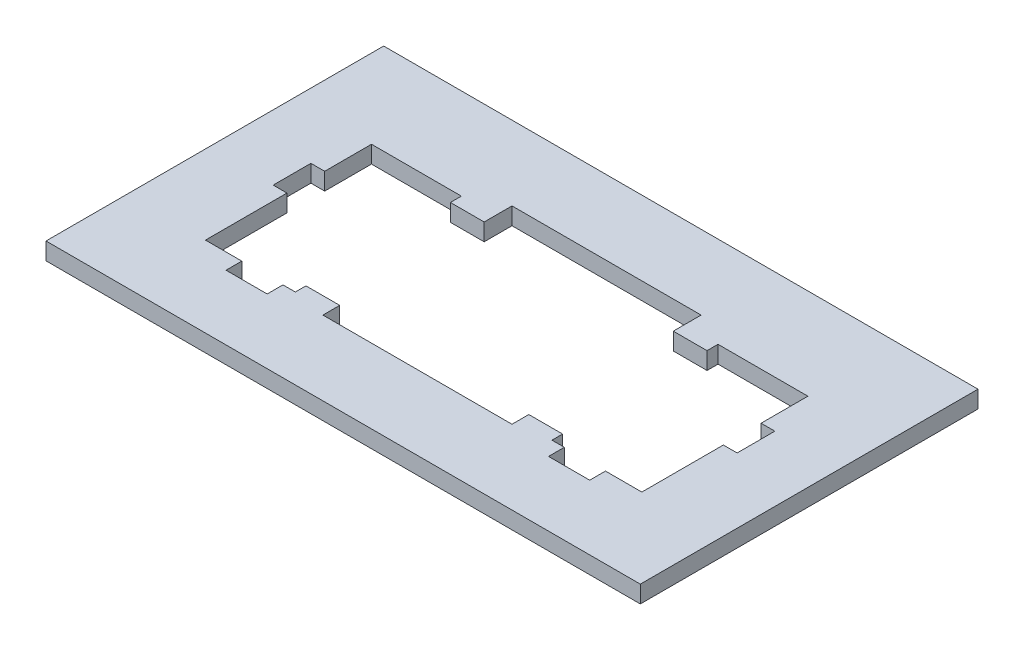
SolidWorks part; units mm, degrees
ref_plane "Front" through (0, 0, 0) normal (0, 0, 1) x (1, 0, 0)
ref_plane "Top" through (0, 0, 0) normal (0, 1, 0) x (1, 0, 0)
ref_plane "Right" through (0, 0, 0) normal (1, 0, 0) x (0, 0, -1)
sketch "Sketch1" plane through (0, 0, 0) normal (0, 1, 0) x (1, 0, 0)
  line L0 (-7, 4.9392) -> (-9.4996, 4.9392)
  line L1 (-22, 12.5) -> (22, 12.5)
  line L2 (-22, 12.5) -> (-22, -12.5)
  line L3 (-22, -12.5) -> (22, -12.5)
  line L4 (22, 12.5) -> (22, -12.5)
  line L5 (-22, 12.5) -> (22, -12.5) construction
  line L6 (-22, -12.5) -> (22, 12.5) construction
  line L7 (-7, 7) -> (7, 7)
  line L8 (-7, 7) -> (-7, -7)
  line L9 (-7, -7) -> (7, -7)
  line L10 (7, 7) -> (7, -7)
  line L11 (-7, 7) -> (7, -7) construction
  line L12 (-7, -7) -> (7, 7) construction
  line L13 (-9.4996, 4.9392) -> (-9.4996, 5.752)
  line L14 (-9.4996, 5.752) -> (-16.1544, 5.752)
  line L15 (-16.1544, 5.752) -> (-16.1544, 2.286)
  line L16 (-16.1544, 2.286) -> (-17.1742, 2.286)
  line L17 (-17.1742, 2.286) -> (-17.1742, -0.508)
  line L18 (-17.1742, -0.508) -> (-16.1544, -0.508)
  line L19 (-16.1544, -0.508) -> (-16.1544, -6.5416)
  line L20 (-16.1544, -6.5416) -> (-13.462, -6.5416)
  line L21 (-13.462, -6.5416) -> (-13.462, -7.71)
  line L22 (-13.462, -7.71) -> (-10.414, -7.71)
  line L23 (-10.414, -7.71) -> (-10.414, -6.5416)
  line L24 (-10.414, -6.5416) -> (-9.4996, -6.5416)
  line L25 (-9.4996, -6.5416) -> (-9.4996, -5.7542)
  line L26 (-9.4996, -5.7542) -> (-7, -5.7542)
  line L27 (0, 0) -> (-28.61, 0) construction
  line L28 (-11.938, -7.71) -> (-11.938, 13.6054) construction
  line L29 (0, 0) -> (0, 7) construction
  line L30 (9.4996, -5.7542) -> (7, -5.7542)
  line L31 (7, 4.9392) -> (9.4996, 4.9392)
  line L32 (9.4996, -6.5416) -> (9.4996, -5.7542)
  line L33 (10.414, -6.5416) -> (9.4996, -6.5416)
  line L34 (10.414, -7.71) -> (10.414, -6.5416)
  line L35 (13.462, -7.71) -> (10.414, -7.71)
  line L36 (13.462, -6.5416) -> (13.462, -7.71)
  line L37 (16.1544, -6.5416) -> (13.462, -6.5416)
  line L38 (16.1544, -0.508) -> (16.1544, -6.5416)
  line L39 (17.1742, -0.508) -> (16.1544, -0.508)
  line L40 (17.1742, 2.286) -> (17.1742, -0.508)
  line L41 (16.1544, 2.286) -> (17.1742, 2.286)
  line L42 (16.1544, 5.752) -> (16.1544, 2.286)
  line L43 (9.4996, 5.752) -> (16.1544, 5.752)
  line L44 (9.4996, 4.9392) -> (9.4996, 5.752)
  line L45 (11.938, -7.71) -> (11.938, 13.6054) construction
  point P0 (0, 0)
  point P6 (0, 0)
  point P50 (0, 0)
  point P51 (0, 0)
  dimension "D1" = 44
  dimension "D2" = 25
  dimension "D3" = 14
  dimension "D4" = 14
  dimension "D5" = 6.6548
  dimension "D6" = 0.8128
  dimension "D7" = 2.794
  dimension "D8" = 0.508
  dimension "D9" = 6.5416
  dimension "D10" = 3.048
  dimension "D11" = 12.2936
  dimension "D12" = 0.7874
  dimension "D13" = 13.462
  dimension "D14" = 23.876
  dimension "D15" = 4.2164
extrude "Boss-Extrude1" add sketch "Sketch1" along normal blind 1.524 contours L4 L1 L2 L3 L31 L44 L43 L42 L41 L40 L39 L38 L37 L36 L35 L34 L33 L32 L30 L10 L9 L8 L26 L25 L24 L23 L22 L21 L20 L19 L18 L17 L16 L15 L14 L13 L0 L7
chamfer "Chamfer1" distance 0.25 angle 45 40 edges at (9.4996, 0, -5.3456) (12.827, 0, -5.752) (16.1544, 0, -4.019) (16.6643, 0, -2.286) (17.1742, 0, -0.889) (16.6643, 0, 0.508) (16.1544, 0, 3.5248) (14.8082, 0, 6.5416) (13.462, 0, 7.1258) (11.938, 0, 7.71) (10.414, 0, 7.1258) (9.9568, 0, 6.5416) (9.4996, 0, 6.1479) (8.2498, 0, 5.7542) (7, 0, 6.3771) (0, 0, 7) (-7, 0, 6.3771) (-8.2498, 0, 5.7542) (-9.4996, 0, 6.1479) (-9.9568, 0, 6.5416) (-10.414, 0, 7.1258) (-11.938, 0, 7.71) (-13.462, 0, 7.1258) (-14.8082, 0, 6.5416) (-16.1544, 0, 3.5248) (-16.6643, 0, 0.508) (-17.1742, 0, -0.889) (-16.6643, 0, -2.286) (-16.1544, 0, -4.019) (-12.827, 0, -5.752) (-9.4996, 0, -5.3456) (-8.2498, 0, -4.9392) (-7, 0, -5.9696) (0, 0, -7) (7, 0, -5.9696) (8.2498, 0, -4.9392) (0, 0, -12.5) (-22, 0, 0) (0, 0, 12.5) (22, 0, 0)
